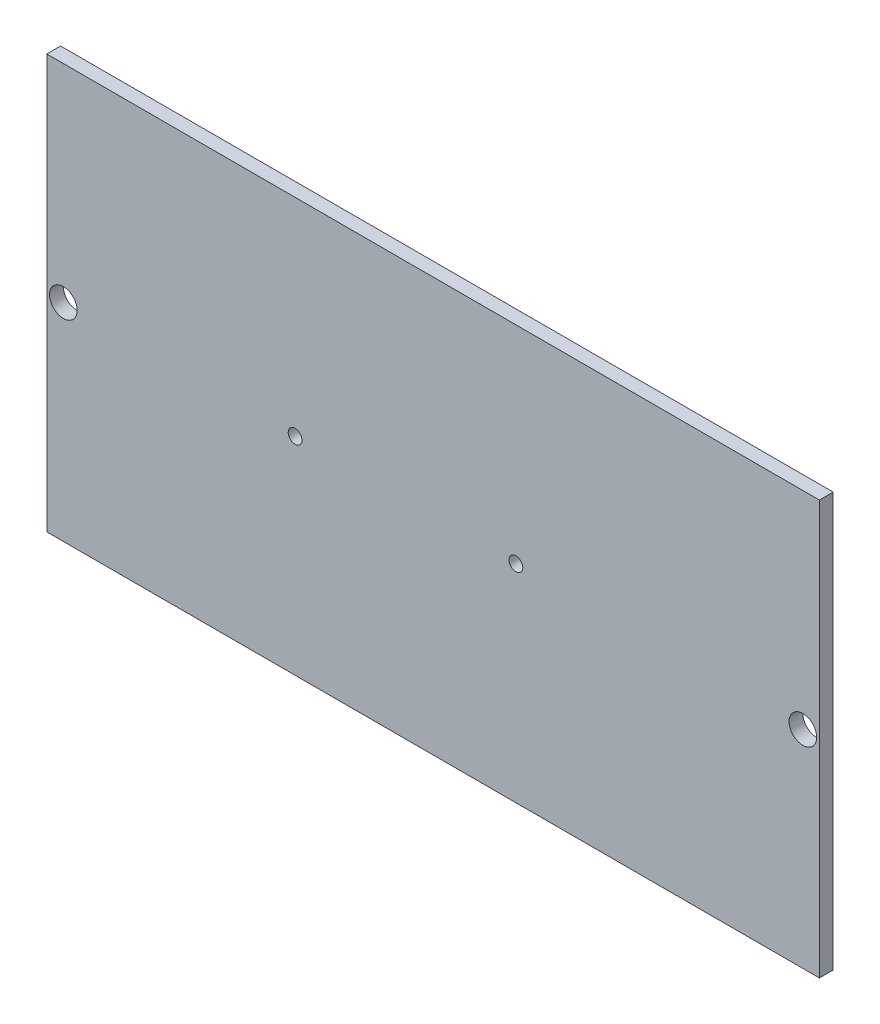
SolidWorks part; units mm, degrees
ref_plane "Plan de face" through (0, 0, 0) normal (0, 0, 1) x (1, 0, 0)
ref_plane "Plan de dessus" through (0, 0, 0) normal (0, 1, 0) x (1, 0, 0)
ref_plane "Plan de droite" through (0, 0, 0) normal (1, 0, 0) x (0, 0, -1)
sketch "Esquisse1" plane through (0, 0, 0) normal (0, 0, 1) x (1, 0, 0)
  line L1 (0, 150) -> (280, 150)
  line L2 (0, 150) -> (0, 0)
  line L3 (0, 0) -> (280, 0)
  line L4 (280, 150) -> (280, 0)
  dimension "D1" = 280
  dimension "D2" = 150
extrude "Boss.-Extru.1" add sketch "Esquisse1" along normal blind 5
sketch "Esquisse2" plane through (0, 0, 5) normal (0, 0, 1) x (1, 0, 0)
  line L0 (90, 75) -> (130.4239, 75) construction
  line L1 (280, 150) -> (0, 150) construction
  line L2 (0, 150) -> (0, 0) construction
  circle A0 centre (90, 75) radius 2.5
  circle A1 centre (170, 75) radius 2.5
  dimension "D1" = 5
  dimension "D2" = 5
  dimension "D3" = 80
  dimension "D4" = 75
  dimension "D5" = 90
extrude "Enlèv. mat.-Extru.1" cut sketch "Esquisse2" against normal blind 5
sketch "Esquisse3" plane through (0, 0, 5) normal (0, 0, 1) x (1, 0, 0)
  line L0 (0, 150) -> (0, 0) construction
  line L1 (280, 150) -> (0, 150) construction
  circle A0 centre (6, 75) radius 5
  dimension "D1" = 10
  dimension "D2" = 6
  dimension "D3" = 75
extrude "Enlèv. mat.-Extru.2" cut sketch "Esquisse3" against normal through all
ref_plane "Plan1" through (140, 0, 0) normal (-1, 0, 0) x (0, 0, 1)
mirror "Symétrie1" about plane through (140, 0, 0) normal (-1, 0, 0) of "Enlèv. mat.-Extru.2"
